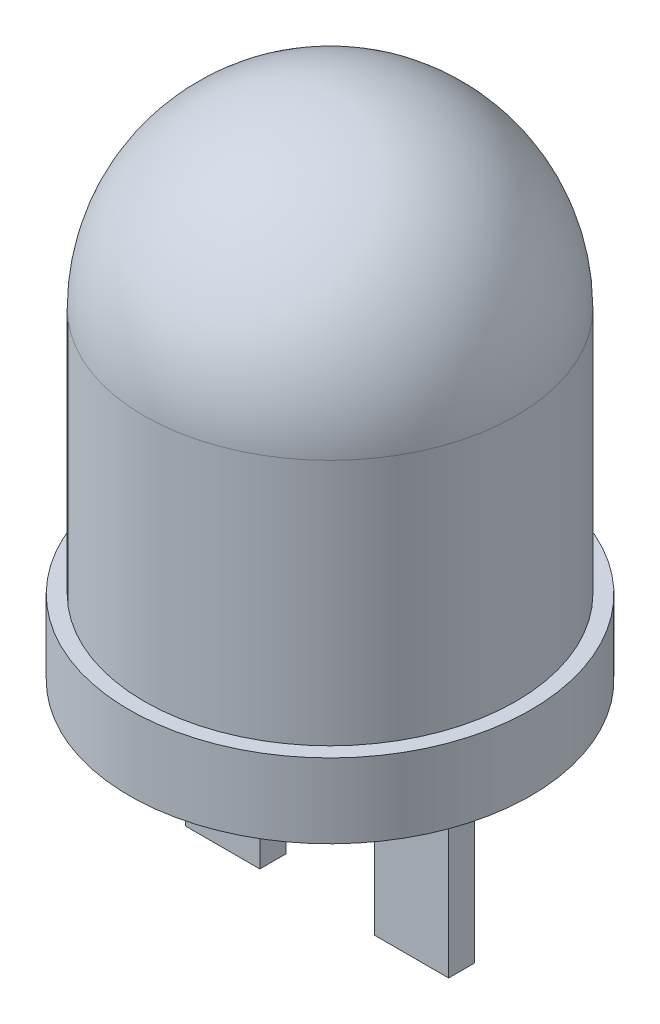
SolidWorks part; units mm, degrees
material "Acrylic (Medium-high impact)"
ref_plane "Front Plane" through (0, 0, 0) normal (0, 0, 1) x (1, 0, 0)
ref_plane "Top Plane" through (0, 0, 0) normal (0, 1, 0) x (1, 0, 0)
ref_plane "Right Plane" through (0, 0, 0) normal (1, 0, 0) x (0, 0, -1)
sketch "Sketch1" plane through (0, 0, 0) normal (0, 0, 1) x (1, 0, 0)
  line L0 (0, 0) -> (0, 13.65)
  line L1 (0, 0) -> (5.4, 0)
  line L2 (5.4, 0) -> (5.4, 2)
  line L3 (5.4, 2) -> (5, 2)
  line L4 (5, 2) -> (5, 8.65)
  arc A0 (5, 8.65) -> (0, 13.65) centre (0, 8.65) ccw
  dimension "D5" = 5
  dimension "D1" = 5.4
  dimension "D2" = 5
  dimension "D3" = 13.65
  dimension "D4" = 2
revolve "Revolve1" add sketch "Sketch1" angle 360 about L0
sketch "Sketch2" plane through (0, 0, 0) normal (0, -1, 0) x (1, 0, 0)
  line L0 (-3.54, 0) -> (-1.54, 0) construction
  line L1 (1.54, 0.35) -> (3.54, 0.35)
  line L2 (1.54, 0.35) -> (1.54, -0.35)
  line L3 (1.54, -0.35) -> (3.54, -0.35)
  line L4 (3.54, 0.35) -> (3.54, -0.35)
  line L5 (-1.54, 0.35) -> (-3.54, 0.35)
  line L6 (-1.54, 0.35) -> (-1.54, -0.35)
  line L7 (-1.54, -0.35) -> (-3.54, -0.35)
  line L8 (-3.54, 0.35) -> (-3.54, -0.35)
  line L9 (-1.54, 0) -> (1.54, 0) construction
  line L10 (1.54, 0) -> (3.54, 0) construction
  line L11 (-2.54, 0.35) -> (-2.54, -0.35) construction
  line L12 (2.54, 0.35) -> (2.54, -0.35) construction
  dimension "D1" = 0.7
  dimension "D2" = 2
  dimension "D3" = 5.08
extrude "Boss-Extrude1" add sketch "Sketch2" along normal blind 5 and the other way blind 5
